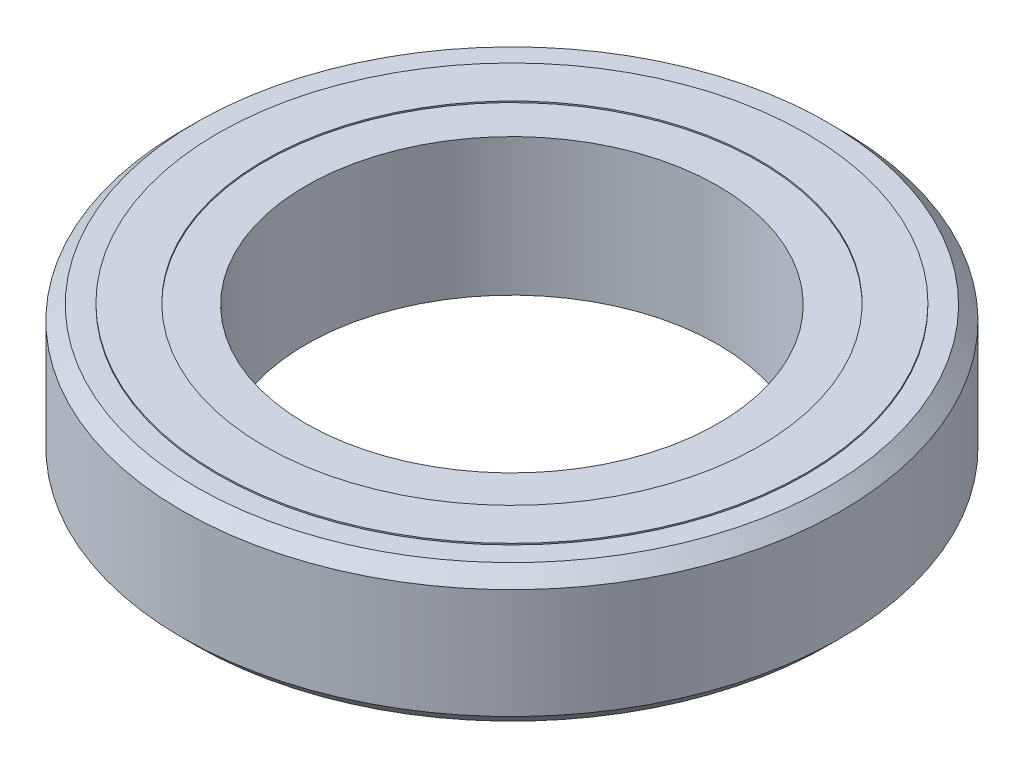
SolidWorks part; units mm, degrees
material "Acero aleado"
ref_plane "Alzado" through (0, 0, 0) normal (0, 0, 1) x (1, 0, 0)
ref_plane "Planta" through (0, 0, 0) normal (0, 1, 0) x (1, 0, 0)
ref_plane "Vista lateral" through (0, 0, 0) normal (1, 0, 0) x (0, 0, -1)
sketch "Croquis1" plane through (0, 0, 0) normal (0, 1, 0) x (1, 0, 0)
  circle A0 centre (0, 0) radius 7.5
  circle A1 centre (0, 0) radius 12
  dimension "D1" = 24
  dimension "D2" = 15
extrude "Saliente-Extruir1" add sketch "Croquis1" along normal mid plane 5
chamfer "Chaflán1" distance 0.5 angle 45 2 edges at (0, -2.5, 12) (0, 2.5, 12)
sketch "Croquis2" plane through (0, 0, 0) normal (0, 1, 0) x (1, 0, 0)
  circle A0 centre (0, 0) radius 9.0164
  circle A1 centre (0, 0) radius 10.7113
extrude "Saliente-Extruir2" add sketch "Croquis2" along normal mid plane 5.1
